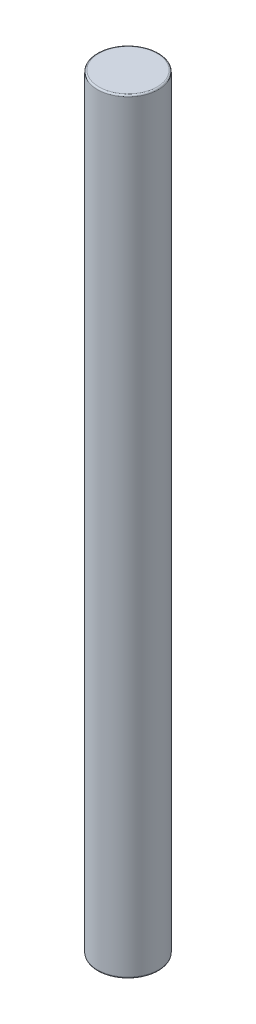
SolidWorks part; units mm, degrees
ref_plane "Front Plane" through (0, 0, 0) normal (0, 0, 1) x (1, 0, 0)
ref_plane "Top Plane" through (0, 0, 0) normal (0, 1, 0) x (1, 0, 0)
ref_plane "Right Plane" through (0, 0, 0) normal (1, 0, 0) x (0, 0, -1)
sketch "Sketch1" plane through (0, 0, 0) normal (0, 1, 0) x (1, 0, 0)
  circle A0 centre (0, 0) radius 4
extrude "Boss-Extrude1" add sketch "Sketch1" along normal blind 100
fillet "Fillet1" radius 0.2 2 edges at (0, 0, 4) (0, 100, 4)
